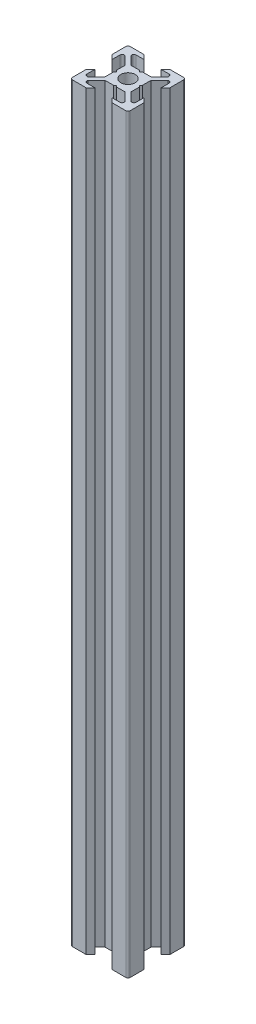
SolidWorks part; units mm, degrees
ref_plane "Face" through (0, 0, 0) normal (0, 0, 1) x (1, 0, 0)
ref_plane "Dessus" through (0, 0, 0) normal (0, 1, 0) x (1, 0, 0)
ref_plane "Droite" through (0, 0, 0) normal (1, 0, 0) x (0, 0, -1)
sketch "Esquisse1" plane through (0, 0, 0) normal (0, 1, 0) x (1, 0, 0)
  line L0 (0, 0) -> (0, 10) construction
  line L1 (0, 0) -> (-10, 0) construction
  line L2 (-10, 0) -> (-10, 10) construction
  line L3 (-10, 10) -> (0, 10) construction
  line L4 (0, 4) -> (-0.5, 4.5)
  line L5 (-0.5, 4.5) -> (-3.4393, 4.5)
  line L6 (-3.4393, 4.5) -> (-6.4393, 7.5)
  line L7 (-6.4393, 7.5) -> (-6.4393, 8.5)
  line L8 (-6.4393, 8.5) -> (-3, 8.5)
  line L9 (-3, 8.5) -> (-4.5, 10)
  line L10 (-4.5, 10) -> (-10, 10)
  line L11 (0, 0) -> (-10, 10) construction
  line L12 (-10, 4.5) -> (-10, 10)
  line L13 (-8.5, 3) -> (-10, 4.5)
  line L14 (-8.5, 6.4393) -> (-8.5, 3)
  line L15 (-7.5, 6.4393) -> (-8.5, 6.4393)
  line L16 (-4.5, 3.4393) -> (-7.5, 6.4393)
  line L17 (-4.5, 0.5) -> (-4.5, 3.4393)
  line L18 (-4, 0) -> (-4.5, 0.5)
  line L19 (0, -4) -> (-0.5, -4.5)
  line L20 (-0.5, -4.5) -> (-3.4393, -4.5)
  line L21 (-4, 0) -> (-4.5, -0.5)
  line L22 (-4.5, -0.5) -> (-4.5, -3.4393)
  line L23 (-4.5, -3.4393) -> (-7.5, -6.4393)
  line L24 (-3.4393, -4.5) -> (-6.4393, -7.5)
  line L25 (-3, -8.5) -> (-4.5, -10)
  line L26 (-6.4393, -8.5) -> (-3, -8.5)
  line L27 (-6.4393, -7.5) -> (-6.4393, -8.5)
  line L28 (-7.5, -6.4393) -> (-8.5, -6.4393)
  line L29 (-4.5, -10) -> (-10, -10)
  line L30 (-10, -4.5) -> (-10, -10)
  line L31 (-8.5, -3) -> (-10, -4.5)
  line L32 (-8.5, -6.4393) -> (-8.5, -3)
  line L33 (8.5, -6.4393) -> (8.5, -3)
  line L34 (8.5, -3) -> (10, -4.5)
  line L35 (10, -4.5) -> (10, -10)
  line L36 (4.5, -10) -> (10, -10)
  line L37 (7.5, -6.4393) -> (8.5, -6.4393)
  line L38 (6.4393, -7.5) -> (6.4393, -8.5)
  line L39 (6.4393, -8.5) -> (3, -8.5)
  line L40 (3, -8.5) -> (4.5, -10)
  line L41 (3.4393, -4.5) -> (6.4393, -7.5)
  line L42 (4.5, -3.4393) -> (7.5, -6.4393)
  line L43 (4.5, -0.5) -> (4.5, -3.4393)
  line L44 (4, 0) -> (4.5, -0.5)
  line L45 (0.5, -4.5) -> (3.4393, -4.5)
  line L46 (0, -4) -> (0.5, -4.5)
  line L47 (4, 0) -> (4.5, 0.5)
  line L48 (4.5, 0.5) -> (4.5, 3.4393)
  line L49 (4.5, 3.4393) -> (7.5, 6.4393)
  line L50 (7.5, 6.4393) -> (8.5, 6.4393)
  line L51 (8.5, 6.4393) -> (8.5, 3)
  line L52 (8.5, 3) -> (10, 4.5)
  line L53 (10, 4.5) -> (10, 10)
  line L54 (4.5, 10) -> (10, 10)
  line L55 (3, 8.5) -> (4.5, 10)
  line L56 (6.4393, 8.5) -> (3, 8.5)
  line L57 (6.4393, 7.5) -> (6.4393, 8.5)
  line L58 (3.4393, 4.5) -> (6.4393, 7.5)
  line L59 (0.5, 4.5) -> (3.4393, 4.5)
  line L60 (0, 4) -> (0.5, 4.5)
  circle A0 centre (0, 0) radius 2.5
  dimension "D10" = 5
  dimension "D1" = 10
  dimension "D2" = 45
  dimension "D3" = 45
  dimension "D4" = 1.5
  dimension "D5" = 7
  dimension "D6" = 1
  dimension "D7" = 4.5
  dimension "D8" = 0.5
  dimension "D9" = 0.75
extrude "Extrusion1" add sketch "Esquisse1" along normal blind 260
fillet "Congé1" radius 0.75 12 edges at (-8.5, 130, -6.4393) (-6.4393, 130, -8.5) (8.5, 130, -6.4393) (6.4393, 130, -8.5) (-8.5, 130, 6.4393) (-6.4393, 130, 8.5) (8.5, 130, 6.4393) (6.4393, 130, 8.5) (10, 130, -10) (-10, 130, -10) (-10, 130, 10) (10, 130, 10)
